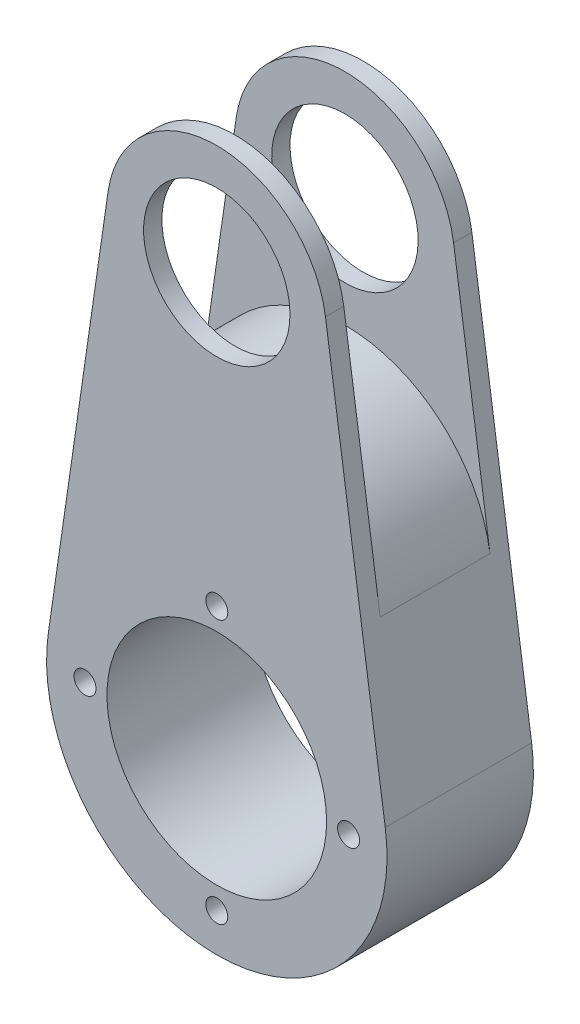
SolidWorks part; units mm, degrees
ref_plane "Alzado" through (0, 0, 0) normal (0, 0, 1) x (1, 0, 0)
ref_plane "Planta" through (0, 0, 0) normal (0, 1, 0) x (1, 0, 0)
ref_plane "Vista lateral" through (0, 0, 0) normal (1, 0, 0) x (0, 0, -1)
sketch "Croquis1" plane through (0, 0, 0) normal (0, 0, 1) x (1, 0, 0)
  line L0 (0, -17.338) -> (0, 18.662) construction
  line L1 (18, 0.662) -> (-18, 0.662) construction
  line L2 (0, 0.662) -> (0, 58.162) construction
  line L3 (-23.0094, 3.9979) -> (-14.8448, 60.3142)
  line L5 (23.0094, 3.9979) -> (14.8448, 60.3142)
  circle A0 centre (0, 0.662) radius 15
  circle A2 centre (0, 18.662) radius 1.5
  circle A3 centre (18, 0.662) radius 1.5
  circle A4 centre (0, -17.338) radius 1.5
  circle A5 centre (-18, 0.662) radius 1.5
  arc A6 (14.8448, 60.3142) -> (-14.8448, 60.3142) centre (0, 58.162) ccw
  arc A7 (-23.0094, 3.9979) -> (23.0094, 3.9979) centre (0, 0.662) ccw
  circle A8 centre (0, 58.162) radius 10
  point P7 (0, 0.662)
  point P11 (0, 0.662)
  point P16 (0, 0)
  point P21 (0, 0)
  point P22 (0, 0)
  point P24 (0, 0.662)
  dimension "D1" = 46.5
  dimension "D2" = 30
  dimension "D4" = 3
  dimension "D6" = 30
  dimension "D7" = 20
  dimension "D3" = 18
  dimension "D5" = 57.5
extrude "Saliente-Extruir1" add sketch "Croquis1" along normal mid plane 20
sketch "Croquis3" plane through (0, 0, 0) normal (1, 0, 0) x (0, 0, -1)
  line L0 (0, 73.162) -> (7.5, 73.162)
  line L1 (10, 73.162) -> (-10, 73.162) construction
  line L2 (7.5, 73.162) -> (7.5, 43.162)
  line L3 (7.5, 43.162) -> (-7.5, 43.162)
  line L4 (-7.5, 43.162) -> (-7.5, 73.162)
  line L5 (-7.5, 73.162) -> (0, 73.162)
  dimension "D1" = 15
  dimension "D2" = 30
extrude "Cortar-Extruir2" cut sketch "Croquis3" against normal through all both and the other way through all
fillet "Redondeo3" radius 20 2 edges at (17.3315, 43.162, 0) (-17.3315, 43.162, 0)
